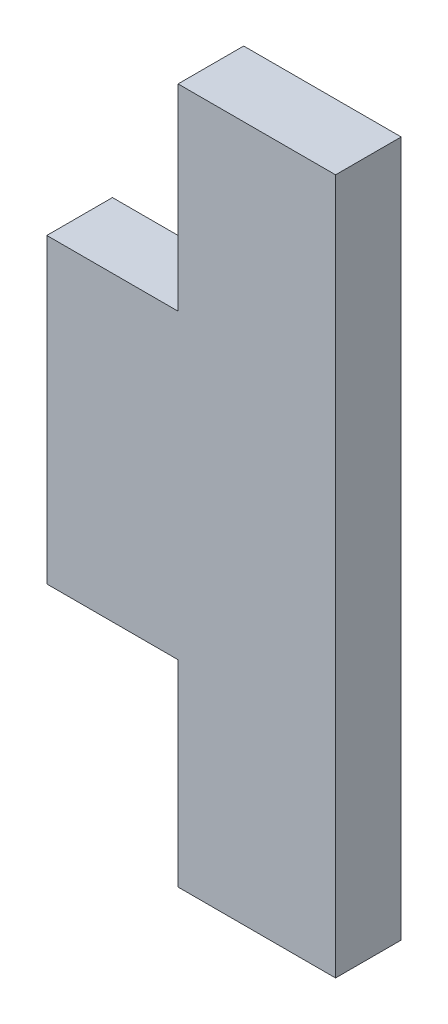
SolidWorks part; units mm, degrees
ref_plane "Front Plane" through (0, 0, 0) normal (0, 0, 1) x (1, 0, 0)
ref_plane "Top Plane" through (0, 0, 0) normal (0, 1, 0) x (1, 0, 0)
ref_plane "Right Plane" through (0, 0, 0) normal (1, 0, 0) x (0, 0, -1)
sketch "Sketch1" plane through (0, 0, 0) normal (0, 0, 1) x (1, 0, 0)
  line L0 (0, 0) -> (1.27, 0) construction
  line L1 (-1.27, -2.921) -> (1.27, -2.921)
  line L2 (-1.27, -2.921) -> (-1.27, 2.921)
  line L3 (-1.27, 2.921) -> (1.27, 2.921)
  line L4 (1.27, -2.921) -> (1.27, 2.921)
  line L5 (-1.27, -2.921) -> (1.27, 2.921) construction
  line L6 (-1.27, 2.921) -> (1.27, -2.921) construction
  line L7 (1.27, -6.731) -> (4.318, -6.731)
  line L8 (1.27, -6.731) -> (1.27, 6.731)
  line L9 (1.27, 6.731) -> (4.318, 6.731)
  line L10 (4.318, -6.731) -> (4.318, 6.731)
  point P0 (0, 0)
  dimension "D1" = 3.048
  dimension "D2" = 2.54
  dimension "D3" = 13.462
  dimension "D4" = 3.81
extrude "Boss-Extrude1" add sketch "Sketch1" along normal blind 1.27 contours L7 L10 L9 L8 L4 | L1 L4 L3 L2
